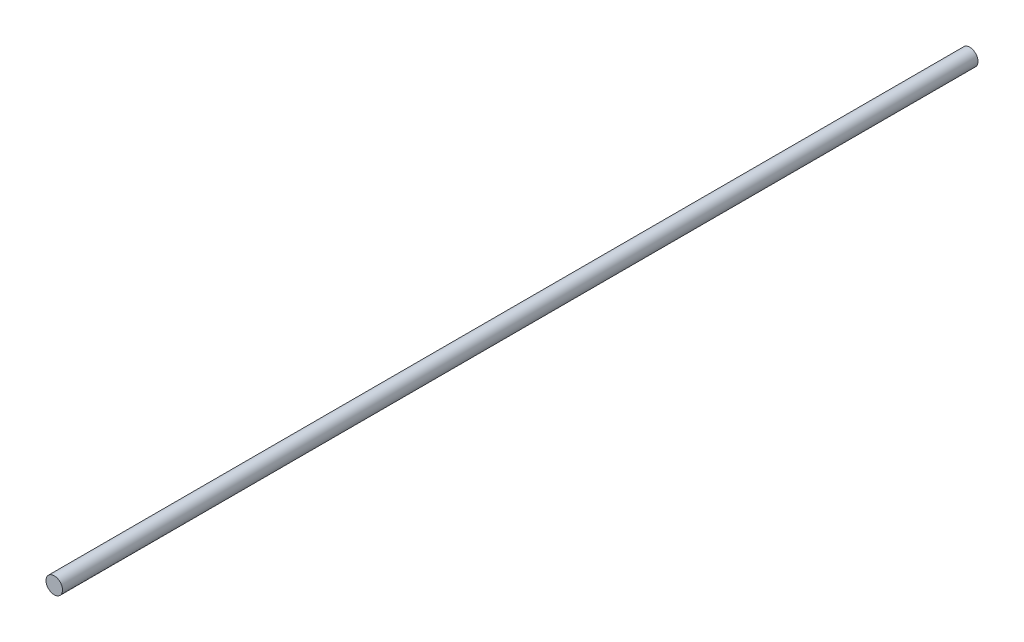
SolidWorks part; units mm, degrees
ref_plane "Front Plane" through (0, 0, 0) normal (0, 0, 1) x (1, 0, 0)
ref_plane "Top Plane" through (0, 0, 0) normal (0, 1, 0) x (1, 0, 0)
ref_plane "Right Plane" through (0, 0, 0) normal (1, 0, 0) x (0, 0, -1)
sketch "Sketch1" plane through (0, 0, 0) normal (0, 0, 1) x (1, 0, 0)
  circle A0 centre (-4.8769, 119.437) radius 3.7971
  dimension "D1" = 7.5942
extrude "Boss-Extrude1" add sketch "Sketch1" along normal up to surface (421.0526 mm away)
